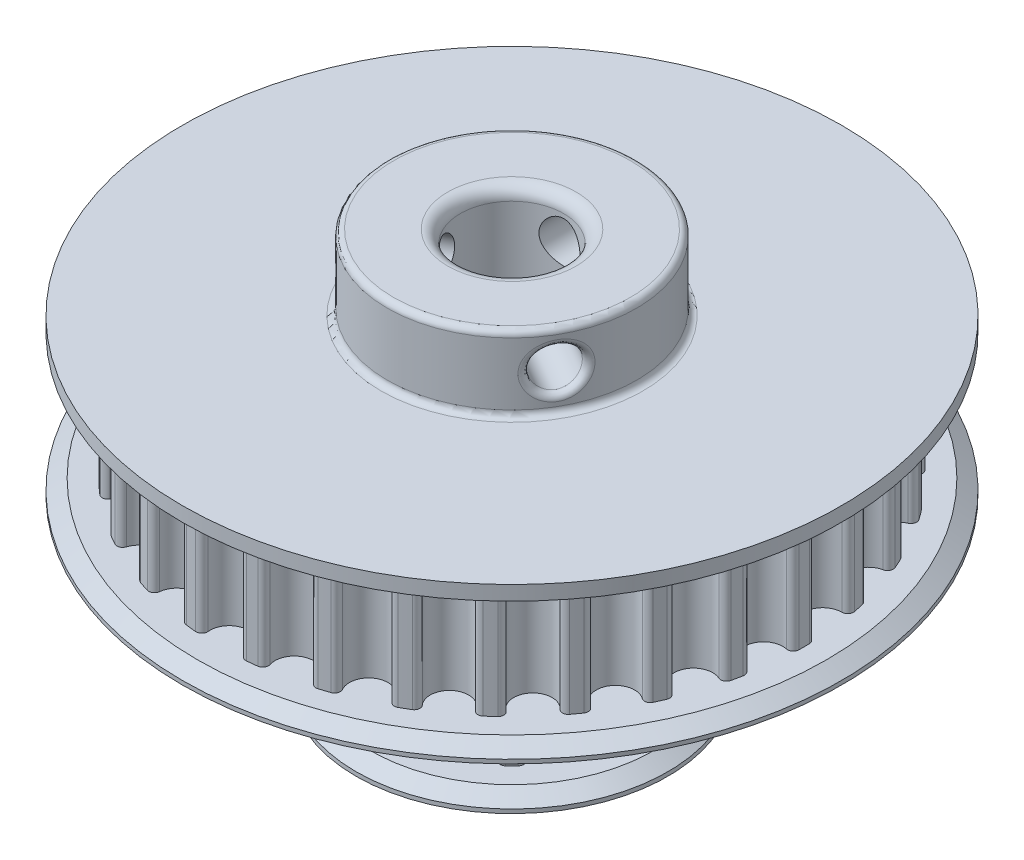
SolidWorks part; units mm, degrees
ref_plane "Plan de face" through (0, 0, 0) normal (0, 0, 1) x (1, 0, 0)
ref_plane "Plan de dessus" through (0, 0, 0) normal (0, 1, 0) x (1, 0, 0)
ref_plane "Plan de droite" through (0, 0, 0) normal (1, 0, 0) x (0, 0, -1)
sketch "Esquisse1" plane through (0, 0, 0) normal (0, 1, 0) x (1, 0, 0)
  line L0 (0, 0) -> (-2.449, 23.3007)
  line L2 (2.449, 23.3007) -> (0, 0)
  line L3 (0, 23.429) -> (0, 0) construction
  line L4 (-2.449, 23.3007) -> (2.449, 23.3007) construction
  circle A1 centre (0, 0) radius 23.429 construction
  arc A2 (-1.5343, 22.836) -> (1.5343, 22.836) centre (0, 22.672) ccw
  arc A3 (-2.449, 23.3007) -> (-2.0293, 23.341) centre (0, 0) cw
  arc A4 (-2.0293, 23.341) -> (-1.5343, 22.836) centre (-1.9897, 22.8847) cw
  arc A5 (2.449, 23.3007) -> (2.0293, 23.341) centre (0, 0) ccw
  arc A6 (2.0293, 23.341) -> (1.5343, 22.836) centre (1.9897, 22.8847) ccw
  arc A7 (-1.5343, 22.836) -> (-1.3662, 23.3892) centre (0, 22.672) cw construction
  arc A8 (1.5343, 22.836) -> (1.3662, 23.3892) centre (0, 22.672) ccw construction
  point P6 (0, 21.129)
  dimension "D2" = 1.543
  dimension "D3" = 0.458
  dimension "D1" = 4.898
  dimension "D4" = 2.3
  dimension "D5" = 12
extrude "Boss.-Extru.1" add sketch "Esquisse1" along normal blind 9.3
pattern_circular "Répétition circulaire1" count 30 over 360 about axis through (0, 0, 0) along (0, 1, 0) of "Boss.-Extru.1"
ref_plane "Plan1" through (0, 4.65, 0) normal (0, -1, 0) x (-1, 0, 0)
sketch "Esquisse2" plane through (0, 9.3, 0) normal (0, 1, 0) x (1, 0, 0)
  circle A0 centre (0, 0) radius 26.429
  arc A1 (22.8257, -5.2827) -> (23.001, -4.458) centre (0, 0) ccw construction
  dimension "D1" = 3
extrude "Boss.-Extru.2" add sketch "Esquisse2" along normal blind 2
mirror "Symétrie1" about plane through (0, 4.65, 0) normal (0, -1, 0) of "Boss.-Extru.2"
sketch "Esquisse4" plane through (0, 11.3, 0) normal (0, 1, 0) x (1, 0, 0)
  circle A0 centre (0, 0) radius 10
  dimension "D1" = 20
extrude "Boss.-Extru.3" add sketch "Esquisse4" along normal blind 6
sketch "Esquisse5" plane through (0, 0, 0) normal (0, 0, 1) x (1, 0, 0)
  line L0 (0, 0) -> (0, 14.3) construction
  line L1 (10, 17.3) -> (-10, 17.3) construction
  circle A0 centre (0, 14.3) radius 1.65
  dimension "D2" = 3.3
  dimension "D1" = 3
extrude "Enlèv. mat.-Extru.2" cut sketch "Esquisse5" against normal through all
pattern_circular "Répétition circulaire2" count 3 over 360 about axis through (0, 17.3, 0) along (0, -1, 0) of "Enlèv. mat.-Extru.2"
sketch "Esquisse10" plane through (0, -2, 0) normal (0, -1, 0) x (1, 0, 0)
  circle A0 centre (0, 0) radius 12.5034
extrude "Boss.-Extru.6" add sketch "Esquisse10" along normal blind 2
sketch "Esquisse7" plane through (0, -4, 0) normal (0, 1, 0) x (1, 0, 0)
  line L0 (0, 0) -> (-2.449, 9.1398)
  line L2 (2.449, 9.1398) -> (0, 0)
  line L3 (0, 9.4622) -> (0, 0) construction
  line L4 (-2.449, 9.1398) -> (2.449, 9.1398) construction
  circle A1 centre (0, 0) radius 9.4622 construction
  arc A2 (-1.5419, 8.7624) -> (1.5419, 8.7624) centre (0, 8.7052) ccw
  arc A3 (-2.449, 9.1398) -> (-2.1013, 9.2259) centre (0, 0) cw
  arc A4 (-2.1013, 9.2259) -> (-1.5419, 8.7624) centre (-1.9996, 8.7794) cw
  arc A5 (2.449, 9.1398) -> (2.1013, 9.2259) centre (0, 0) ccw
  arc A6 (2.1013, 9.2259) -> (1.5419, 8.7624) centre (1.9996, 8.7794) ccw
  arc A7 (-1.5419, 8.7624) -> (-1.3979, 9.3584) centre (0, 8.7052) cw construction
  arc A8 (1.5419, 8.7624) -> (1.3979, 9.3584) centre (0, 8.7052) ccw construction
  point P2 (0, 7.1622)
  dimension "D1" = 1.543
  dimension "D2" = 0.458
  dimension "D3" = 2.3
  dimension "D4" = 4.898
  dimension "D5" = 30
extrude "Boss.-Extru.4" add sketch "Esquisse7" against normal blind 9.3
pattern_circular "Répétition circulaire3" count 12 over 360 about axis through (0, 0, 0) along (0, 1, 0) of "Boss.-Extru.4"
ref_plane "Plan2" through (0, -8.65, 0) normal (0, 1, 0) x (1, 0, 0)
sketch "Esquisse9" plane through (0, -4, 0) normal (0, 1, 0) x (1, 0, 0)
  circle A0 centre (0, 0) radius 12.5034
  circle A2 centre (0, 0) radius 12.5034 construction
extrude "Boss.-Extru.5" add sketch "Esquisse9" along normal blind 2
mirror "Symétrie2" about plane through (0, -8.65, 0) normal (0, 1, 0) of "Boss.-Extru.5"
chamfer "Chanfrein1" distance 1.2 angle 35 6 edges at (0, 9.3, 26.429) (0, 0, 26.429) (0, -15.3, 12.5034) (0, -13.3, 12.5034) (0, -2, 26.429) (0, -4, -12.5034)
sketch "Esquisse3" plane through (0, 17.3, 0) normal (0, 1, 0) x (1, 0, 0)
  circle A0 centre (0, 0) radius 4.15
  dimension "D1" = 8.3
extrude "Enlèv. mat.-Extru.3" cut sketch "Esquisse3" against normal through all contours A0
fillet "Congé2" radius 0.5 5 edges at (0, 11.3, 10) (0, 17.3, 10) (0.3544, 12.6885, -9.9937) (-7.7413, 13.9455, 6.3302) (9.3528, 13.9455, 3.5391)
fillet "Congé3" radius 1 2 edges at (0, 17.3, 4.15) (0, -15.3, 4.15)
equation "\"nb_tooth1\"= 30"
equation "\"D5@Esquisse1\"=360/\"nb_tooth1\""
equation "\"D1@Répétition circulaire1\"=\"nb_tooth1\""
equation "\"nb_tooth2\"= 12"
equation "\"D5@Esquisse7\"=360/\"nb_tooth2\""
equation "\"D1@Répétition circulaire3\"=\"nb_tooth2\""
